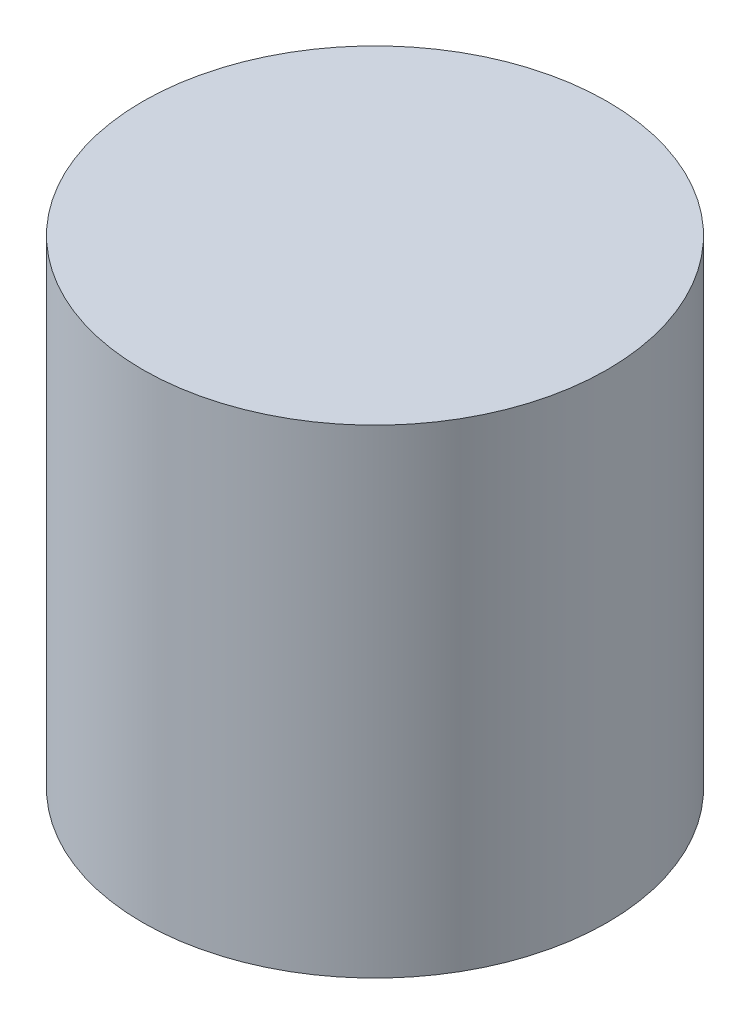
SolidWorks part; units mm, degrees
ref_plane "Front Plane" through (0, 0, 0) normal (0, 0, 1) x (1, 0, 0)
ref_plane "Top Plane" through (0, 0, 0) normal (0, 1, 0) x (1, 0, 0)
ref_plane "Right Plane" through (0, 0, 0) normal (1, 0, 0) x (0, 0, -1)
ref_plane "Plane1" through (0, 32.75, 0) normal (0, 1, 0) x (1, 0, 0)
sketch "Sketch1" plane through (0, 32.75, 0) normal (0, 1, 0) x (1, 0, 0)
  circle B0 centre (287.1745, 235) radius 49
sketch_block_instance "Block1-1"
sketch_block "Block1"
extrude "Boss-Extrude1" add sketch "Sketch1" against normal blind 101
